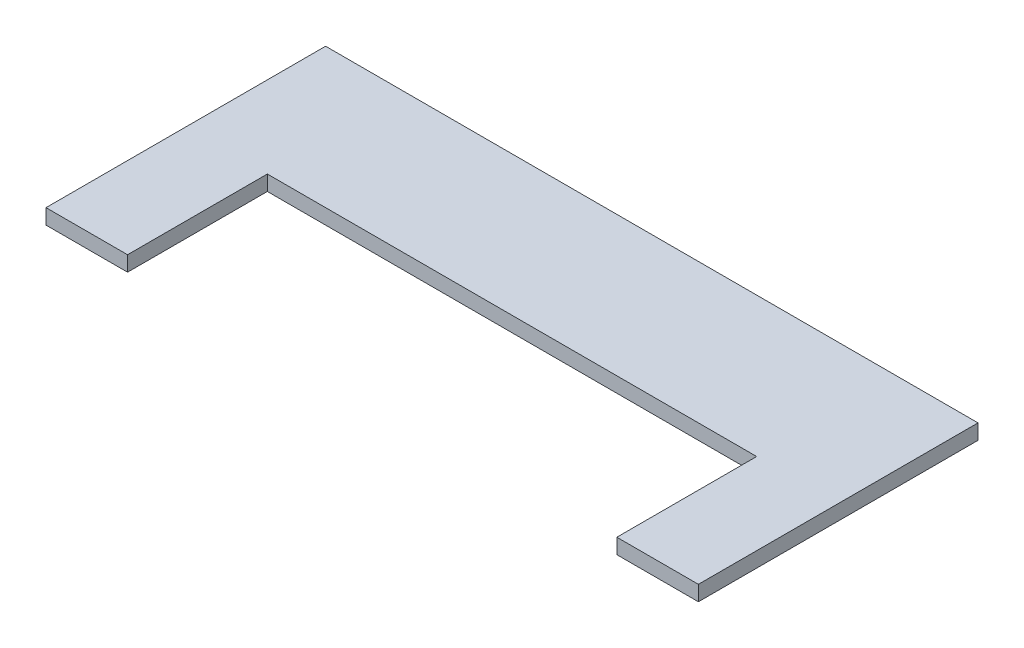
SolidWorks part; units mm, degrees
ref_plane "Front Plane" through (0, 0, 0) normal (0, 0, 1) x (1, 0, 0)
ref_plane "Top Plane" through (0, 0, 0) normal (0, 1, 0) x (1, 0, 0)
ref_plane "Right Plane" through (0, 0, 0) normal (1, 0, 0) x (0, 0, -1)
sketch "Sketch1" plane through (0, 0, 0) normal (0, 1, 0) x (1, 0, 0)
  line L0 (0, 0) -> (0, 120)
  line L1 (0, 120) -> (280, 120)
  line L2 (280, 120) -> (280, 0)
  line L3 (280, 0) -> (245, 0)
  line L4 (245, 0) -> (245, 60)
  line L5 (0, 0) -> (35, 0)
  line L6 (35, 0) -> (35, 60)
  line L7 (35, 60) -> (245, 60)
extrude "Boss-Extrude1" add sketch "Sketch1" along normal blind 6.5
